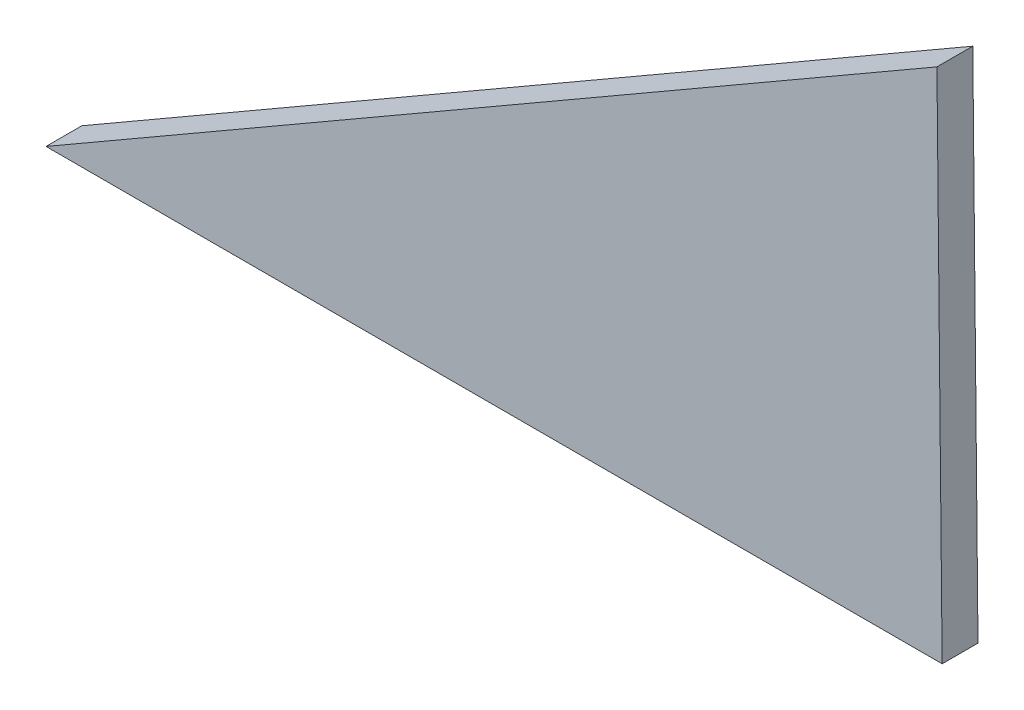
SolidWorks part; units mm, degrees
ref_plane "Front Plane" through (0, 0, 0) normal (0, 0, 1) x (1, 0, 0)
ref_plane "Top Plane" through (0, 0, 0) normal (0, 1, 0) x (1, 0, 0)
ref_plane "Right Plane" through (0, 0, 0) normal (1, 0, 0) x (0, 0, -1)
sketch "Sketch1" plane through (0, 0, 0) normal (0, 0, 1) x (1, 0, 0)
  line L0 (-46.5726, -38.82) -> (53.4274, -38.82)
  line L1 (-46.5726, -38.82) -> (52.8456, 18.5792)
  line L3 (52.8456, 18.5792) -> (53.4274, -38.82)
extrude "Boss-Extrude1" add sketch "Sketch1" along normal blind 4
